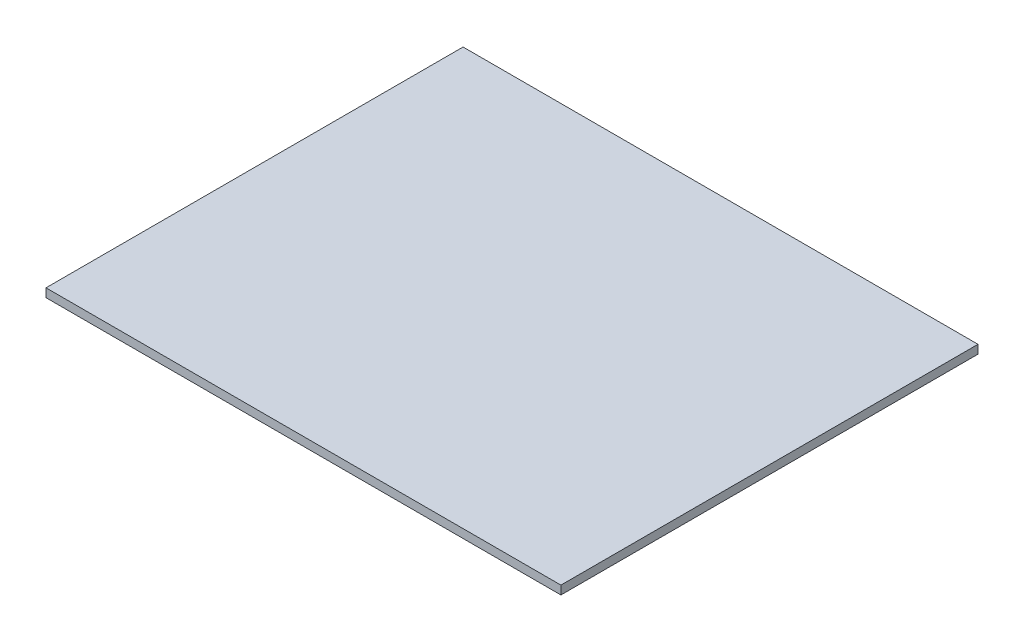
SolidWorks part; units mm, degrees
ref_plane "Plane1" through (0, 0, 0) normal (0, 0, 1) x (1, 0, 0)
ref_plane "Plane2" through (0, 0, 0) normal (0, 1, 0) x (1, 0, 0)
ref_plane "Plane3" through (0, 0, 0) normal (1, 0, 0) x (0, 0, -1)
sketch "Sketch1" plane through (0, 0, 0) normal (0, 1, 0) x (1, 0, 0)
  line L1 (0, 0) -> (600, 0)
  line L2 (0, 0) -> (0, 486)
  line L3 (0, 486) -> (600, 486)
  line L4 (600, 0) -> (600, 486)
  dimension "D1" = 486
  dimension "D2" = 600
extrude "Boss-Extrude1" add sketch "Sketch1" along normal blind 10
